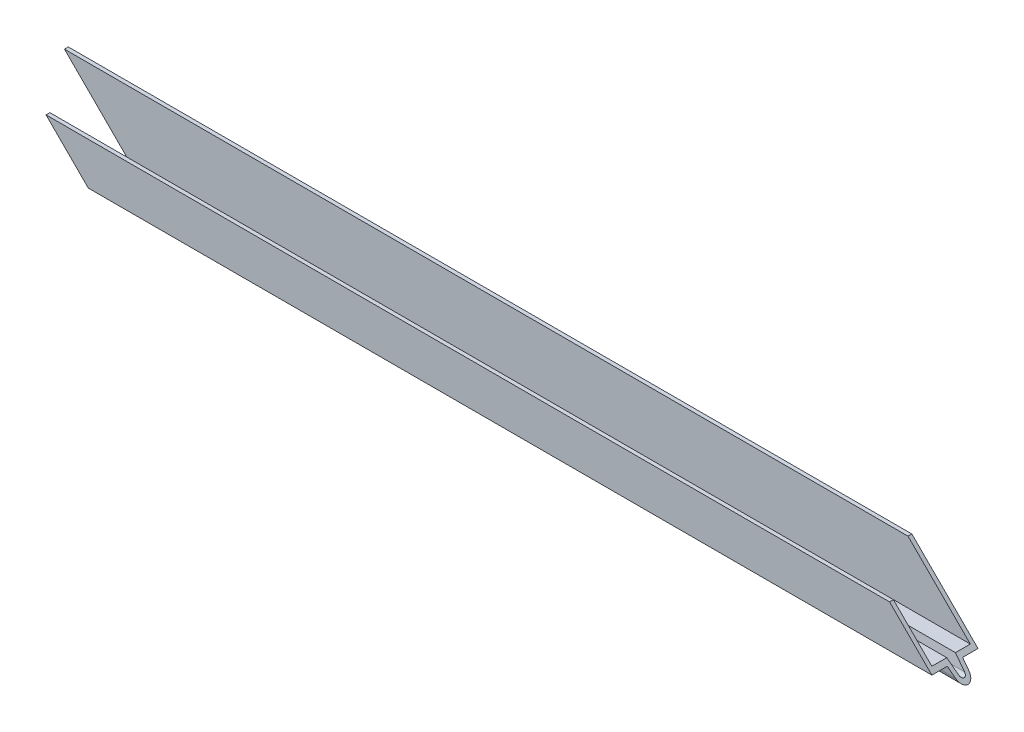
SolidWorks part; units mm, degrees
material "6063-O"
ref_plane "Front Plane" through (0, 0, 0) normal (0, 0, 1) x (1, 0, 0)
ref_plane "Top Plane" through (0, 0, 0) normal (0, 1, 0) x (1, 0, 0)
ref_plane "Right Plane" through (0, 0, 0) normal (1, 0, 0) x (0, 0, -1)
other "Configuration Table"
sketch "Sketch1" plane through (0, 0, 0) normal (1, 0, 0) x (0, 0, -1)
  line L0 (7.62, 0) -> (7.62, -21.844)
  line L1 (7.62, -21.844) -> (2.54, -21.844)
  line L2 (-2.54, -21.844) -> (-2.2022, -24.2477)
  line L3 (2.2022, -24.2477) -> (2.54, -21.844)
  line L4 (-2.54, -21.844) -> (-7.62, -21.844)
  line L5 (-7.62, -21.844) -> (-7.62, -7.874)
  line L6 (6.35, 0) -> (6.35, -20.574)
  line L7 (6.35, -20.574) -> (1.436, -20.574)
  line L8 (0.9445, -24.0709) -> (1.436, -20.574)
  line L9 (-1.436, -20.574) -> (-0.9445, -24.0709)
  line L10 (-1.436, -20.574) -> (-6.35, -20.574)
  line L11 (-6.35, -20.574) -> (-6.35, -7.874)
  line L12 (7.62, 0) -> (6.35, 0)
  line L13 (-7.62, -7.874) -> (-6.35, -7.874)
  line L14 (0, 0) -> (0, -30.4009) construction
  arc A0 (-2.2022, -24.2477) -> (2.2022, -24.2477) centre (0, -23.9382) ccw
  arc A1 (-0.9445, -24.0709) -> (0.9445, -24.0709) centre (0, -23.9382) ccw
  dimension "D1" = 15.24
  dimension "D2" = 4.318
  dimension "D3" = 21.844
  dimension "D4" = 13.97
  dimension "D5" = 12.7
  dimension "D6" = 82
  dimension "D7" = 5.08
extrude "Boss-Extrude1" add sketch "Sketch1" along normal mid plane 304.8
sketch "Sketch9" plane through (0, 0, 7.62) normal (0, 0, 1) x (1, 0, 0)
  line L0 (-152.4, -26.162) -> (-126.238, 0)
  line L1 (152.4, 0) -> (-152.4, 0) construction
  line L2 (-126.238, 0) -> (-152.4, 0)
  line L3 (-152.4, 0) -> (-152.4, -26.162)
extrude "Cut-Front-Left-Top" [suppressed] cut sketch "Sketch9" against normal through all
sketch "Sketch12" plane through (0, 0, 7.62) normal (0, 0, 1) x (1, 0, 0)
  line L0 (-152.4, 0) -> (-126.238, -26.162)
  line L1 (-152.4, -26.162) -> (152.4, -26.162) construction
  line L2 (-126.238, -26.162) -> (-152.4, -26.162)
  line L3 (-152.4, -26.162) -> (-152.4, 0)
extrude "Cut-Front-Left-Bottom" cut sketch "Sketch12" against normal through all
sketch "Sketch4" plane through (0, 0, 0) normal (0, 1, 0) x (1, 0, 0)
  line L0 (-296.672, 7.62) -> (-281.432, -7.62)
  line L1 (152.4, -7.62) -> (-144.526, -7.62) construction
  line L2 (-281.432, -7.62) -> (-296.672, -7.62)
  line L3 (-296.672, -7.62) -> (-296.672, 7.62)
extrude "Cut-Top-Left-Front" [suppressed] cut sketch "Sketch4" against normal through all
sketch "Sketch7" plane through (0, 0, 7.62) normal (0, 0, 1) x (1, 0, 0)
  line L0 (152.4, -26.162) -> (126.238, 0)
  line L2 (126.238, 0) -> (152.4, 0)
  line L4 (152.4, 0) -> (152.4, -26.162)
  line L5 (152.4, -7.874) -> (152.4, -21.844) construction
  line L6 (152.4, 0) -> (-152.4, 0) construction
extrude "Cut-Front-Right-Top" cut sketch "Sketch7" against normal through all
sketch "Sketch2" plane through (0, 0, 0) normal (0, 1, 0) x (1, 0, 0)
  line L0 (296.672, 7.62) -> (281.432, -7.62)
  line L1 (134.112, -7.62) -> (-144.526, -7.62) construction
  line L2 (281.432, -7.62) -> (296.672, -7.62)
  line L3 (296.672, -7.62) -> (296.672, 7.62)
extrude "Cut-Top-Right-Front" [suppressed] cut sketch "Sketch2" against normal through all
sketch "Sketch11" plane through (0, 0, 7.62) normal (0, 0, 1) x (1, 0, 0)
  line L0 (296.672, 0) -> (270.51, -26.162)
  line L1 (-126.238, -26.162) -> (152.4, -26.162) construction
  line L2 (270.51, -26.162) -> (296.672, -26.162)
  line L3 (296.672, -26.162) -> (296.672, 0)
extrude "Cut-Front-Right-Bottom" [suppressed] cut sketch "Sketch11" against normal through all
